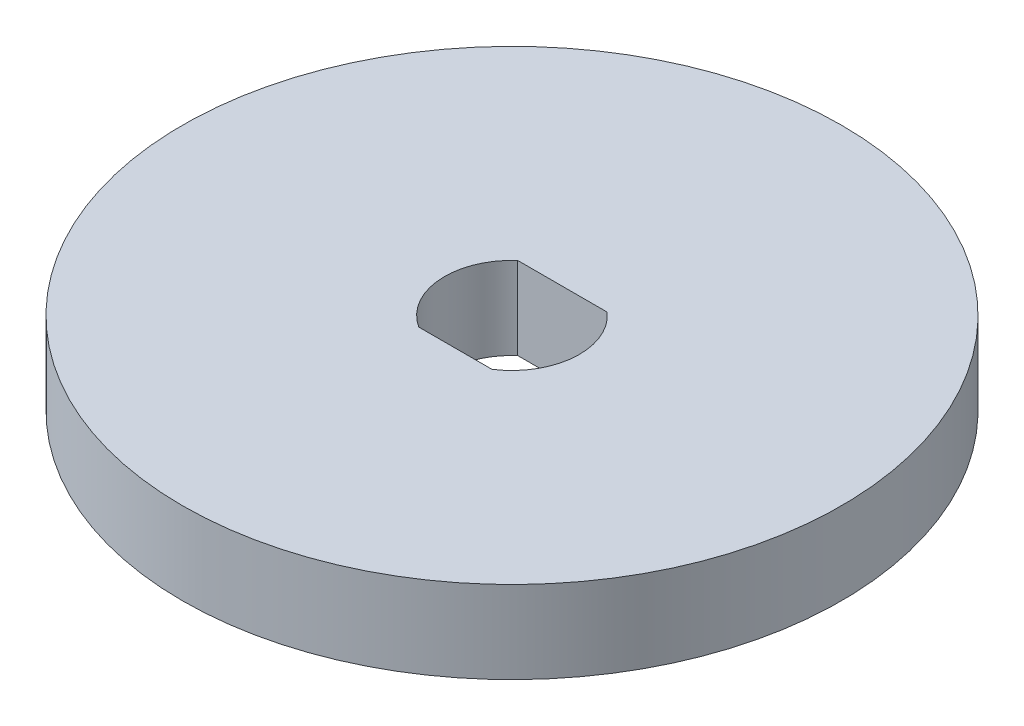
SolidWorks part; units mm, degrees
ref_plane "Front Plane" through (0, 0, 0) normal (0, 0, 1) x (1, 0, 0)
ref_plane "Top Plane" through (0, 0, 0) normal (0, 1, 0) x (1, 0, 0)
ref_plane "Right Plane" through (0, 0, 0) normal (1, 0, 0) x (0, 0, -1)
sketch "Sketch1" plane through (0, 0, 0) normal (0, 1, 0) x (1, 0, 0)
  line L0 (-1.725, 1.9453) -> (1.725, 1.9453)
  line L5 (-1.4097, -2.1847) -> (1.4097, -2.1847)
  arc A4 (-1.725, 1.9453) -> (-1.4097, -2.1847) centre (0, 0) ccw
  circle A8 centre (0, 0) radius 12.7
  arc A9 (1.4097, -2.1847) -> (1.725, 1.9453) centre (0, 0) ccw
  point P0 (0, 0)
  point P6 (-1.3557, 1.6797)
  point P7 (3.2912, -0.5666)
  point P10 (0, 0)
  point P11 (0, 0)
  point P13 (0, 0)
  point P17 (0, 0)
  point P20 (0, 0)
  dimension "D2" = 3.45
  dimension "D5" = 5.2
  dimension "D1" = 25.4
  dimension "D3" = 4.13
extrude "Boss-Extrude1" add sketch "Sketch1" along normal blind 3.175
